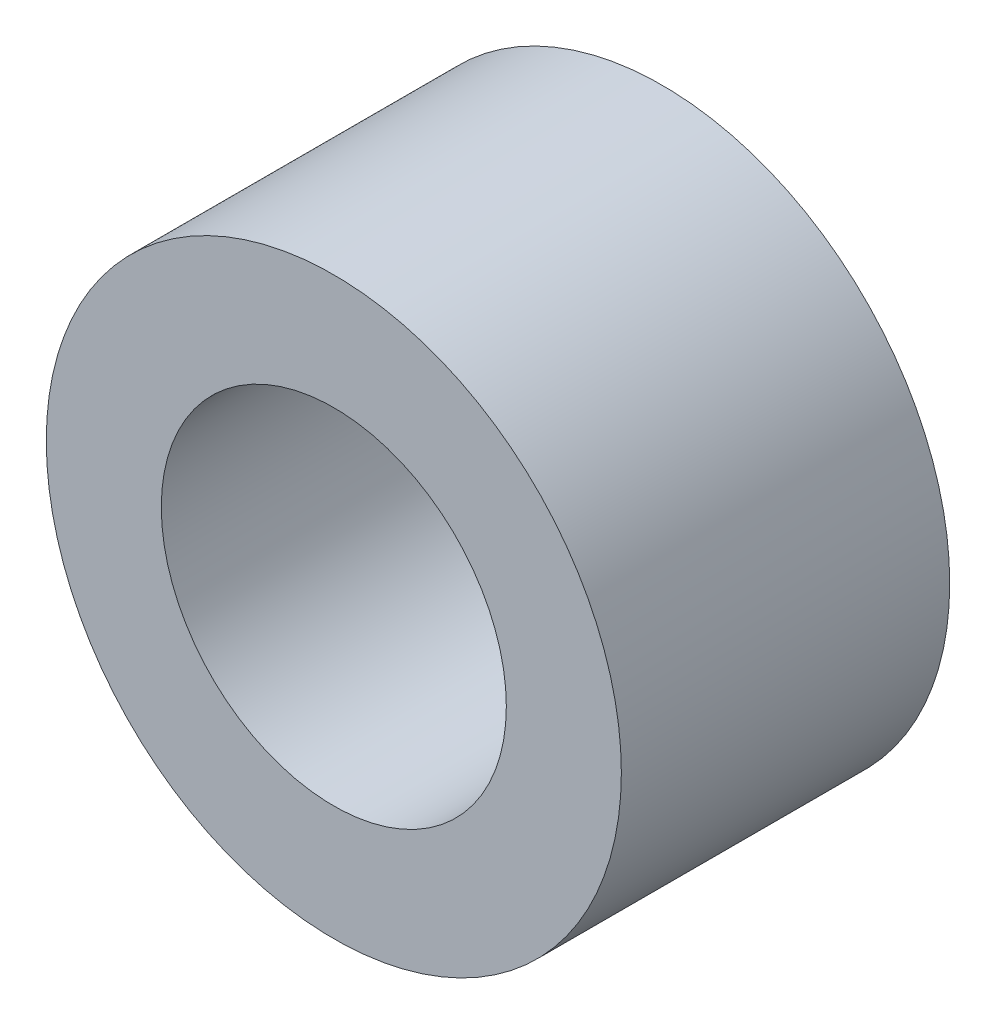
SolidWorks part; units mm, degrees
ref_plane "Front Plane" through (0, 0, 0) normal (0, 0, 1) x (1, 0, 0)
ref_plane "Top Plane" through (0, 0, 0) normal (0, 1, 0) x (1, 0, 0)
ref_plane "Right Plane" through (0, 0, 0) normal (1, 0, 0) x (0, 0, -1)
sketch "Sketch1" plane through (0, 0, 0) normal (0, 0, 1) x (1, 0, 0)
  circle A0 centre (0, 0) radius 12.7
  circle A2 centre (0, 0) radius 7.62
extrude "Boss-Extrude1" add sketch "Sketch1" along normal blind 14.5034
